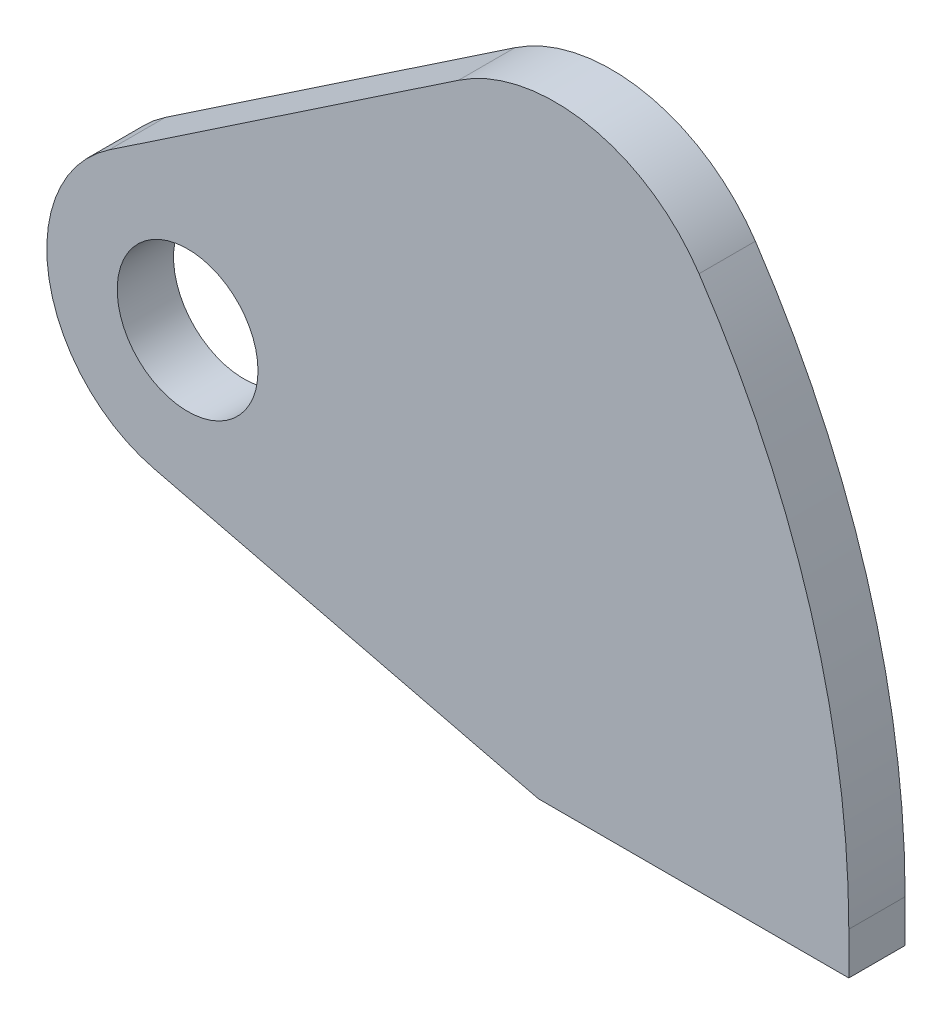
SolidWorks part; units mm, degrees
material "AISI 1020"
ref_plane "Спереди" through (0, 0, 0) normal (0, 0, 1) x (1, 0, 0)
ref_plane "Сверху" through (0, 0, 0) normal (0, 1, 0) x (1, 0, 0)
ref_plane "Справа" through (0, 0, 0) normal (1, 0, 0) x (0, 0, -1)
sketch "Эскиз1" plane through (0, 0, 0) normal (0, 0, 1) x (1, 0, 0)
  line L0 (10.65, 0) -> (10.65, -3) construction
  line L1 (10.65, -3) -> (-11.3978, -3) construction
  line L2 (-11.3978, -3) -> (-38.6779, 3.6515) construction
  line L3 (-17.0651, 38.3617) -> (-41.8901, 21.6646) construction
  line L4 (10.65, 0) -> (10.65, -3)
  line L5 (10.65, -3) -> (-11.3978, -3)
  line L6 (-11.3978, -3) -> (-38.6779, 3.6515)
  line L7 (-17.0651, 38.3617) -> (-41.8901, 21.6646)
  circle A0 centre (-36.3091, 13.3669) radius 5 construction
  arc A1 (0.0148, 34.9997) -> (-17.0651, 38.3617) centre (-10.2026, 28.1586) ccw construction
  arc A2 (10.65, 0) -> (0.0148, 34.9997) centre (-52.2585, 0) ccw construction
  arc A3 (-41.8901, 21.6646) -> (-38.6779, 3.6515) centre (-36.3091, 13.3669) ccw construction
  circle A4 centre (-36.3091, 13.3669) radius 5
  arc A5 (0.0148, 34.9997) -> (-17.0651, 38.3617) centre (-10.2026, 28.1586) ccw
  arc A6 (10.65, 0) -> (0.0148, 34.9997) centre (-52.2585, 0) ccw
  arc A7 (-41.8901, 21.6646) -> (-38.6779, 3.6515) centre (-36.3091, 13.3669) ccw
extrude "Бобышка-Вытянуть1" add sketch "Эскиз1" along normal blind 4
